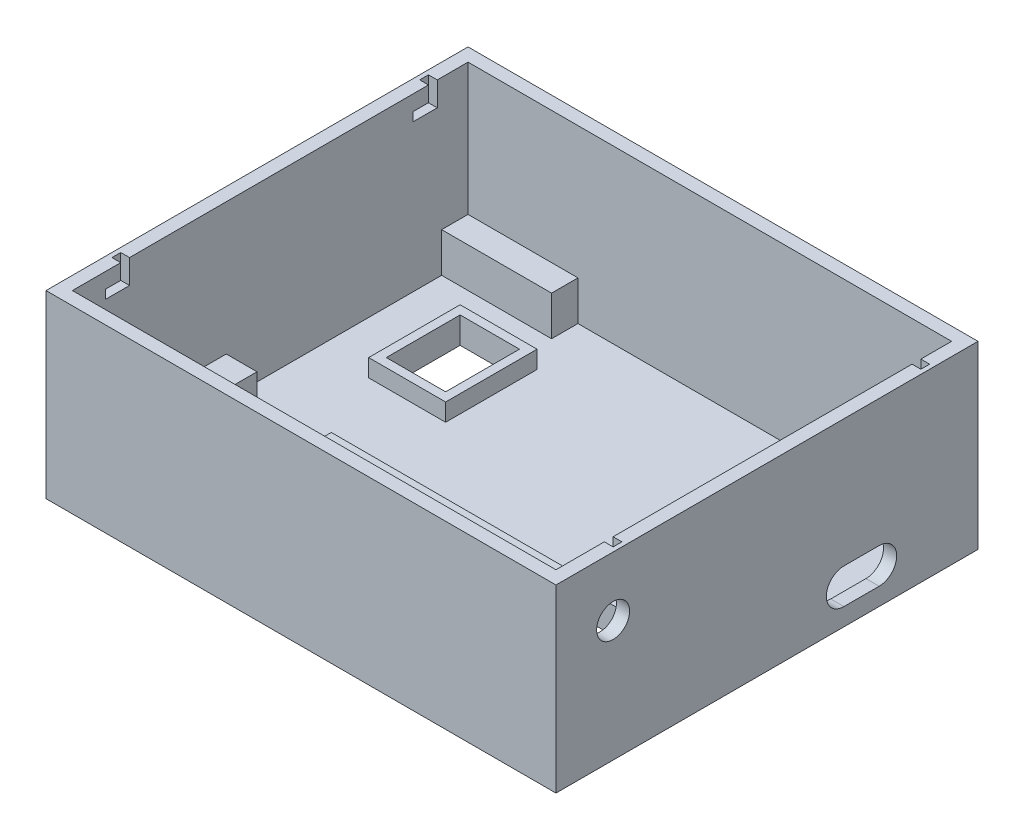
SolidWorks part; units mm, degrees
ref_plane "Front Plane" through (0, 0, 0) normal (0, 0, 1) x (1, 0, 0)
ref_plane "Top Plane" through (0, 0, 0) normal (0, 1, 0) x (1, 0, 0)
ref_plane "Right Plane" through (0, 0, 0) normal (1, 0, 0) x (0, 0, -1)
sketch "Sketch1" plane through (0, 0, 0) normal (0, 1, 0) x (1, 0, 0)
  line L1 (-58, 48) -> (58, 48)
  line L2 (-58, 48) -> (-58, -48)
  line L3 (-58, -48) -> (58, -48)
  line L4 (58, 48) -> (58, -48)
  line L5 (-58, 48) -> (58, -48) construction
  line L6 (-58, -48) -> (58, 48) construction
  point P0 (0, 0)
  dimension "D1" = 116
  dimension "D2" = 96
extrude "Boss-Extrude1" add sketch "Sketch1" along normal blind 6
sketch "Sketch2" plane through (0, 6, 0) normal (0, 1, 0) x (1, 0, 0)
  line L0 (58, 48) -> (-58, 48) construction
  line L1 (-58, -48) -> (58, -48)
  line L2 (-58, -48) -> (-58, 48)
  line L3 (-58, 48) -> (58, 48)
  line L4 (58, -48) -> (58, 48)
  line L5 (-58, -48) -> (58, 48) construction
  line L6 (-58, 48) -> (58, -48) construction
  line L7 (58, -48) -> (58, 48) construction
  line L9 (-55, 45) -> (55, 45)
  line L10 (-55, 45) -> (-55, -45)
  line L11 (-55, -45) -> (55, -45)
  line L12 (55, 45) -> (55, -45)
  line L13 (-55, 45) -> (55, -45) construction
  line L14 (-55, -45) -> (55, 45) construction
  point P0 (0, 0)
  point P10 (0, 0)
  dimension "D1" = 3
  dimension "D2" = 3
extrude "Boss-Extrude2" add sketch "Sketch2" along normal blind 35
sketch "Sketch3" plane through (0, 6, 0) normal (0, 1, 0) x (1, 0, 0)
  line L0 (-55, -45) -> (55, -45) construction
  line L1 (-25.6, -10.5) -> (46, -10.5)
  line L2 (-25.6, -10.5) -> (-25.6, -35)
  line L3 (-25.6, -35) -> (46, -35)
  line L4 (46, -10.5) -> (46, -35)
  line L5 (55, -45) -> (55, 45) construction
  line L7 (-41.1, 29.3) -> (-27.6, 29.3)
  line L8 (-41.1, 29.3) -> (-41.1, 12.5)
  line L9 (-41.1, 12.5) -> (-27.6, 12.5)
  line L10 (-27.6, 29.3) -> (-27.6, 12.5)
  dimension "D1" = 24.5
  dimension "D2" = 71.6
  dimension "D3" = 10
  dimension "D4" = 9
  dimension "D5" = 23
  dimension "D6" = 2
  dimension "D7" = 16.8
  dimension "D8" = 13.5
extrude "Cut-Extrude1" cut sketch "Sketch3" against normal blind 35
sketch "Sketch4" plane through (0, 6, 0) normal (0, 1, 0) x (1, 0, 0)
  line L0 (-25.6, -10.5) -> (-25.6, -35) construction
  line L1 (-30.6, -13.75) -> (-25.6, -13.75)
  line L2 (-30.6, -13.75) -> (-30.6, -31.75)
  line L3 (-30.6, -31.75) -> (-25.6, -31.75)
  line L4 (-25.6, -13.75) -> (-25.6, -31.75)
  point P6 (-25.6, -22.75)
  point P7 (-25.6, -22.75)
  dimension "D1" = 18
  dimension "D2" = 5
extrude "Cut-Extrude2" cut sketch "Sketch4" against normal blind 4
sketch "Sketch5" plane through (0, 0, 0) normal (0, 1, 0) x (1, 0, 0)
  line L0 (0, 9.4044) -> (0, -19.4219) construction
  line L1 (0, -10.5) -> (71.4405, -10.5) construction
  line L2 (46, -10.5) -> (-25.6, -10.5) construction
sketch "Sketch6" plane through (58, 0, 0) normal (1, 0, 0) x (0, 0, -1)
  line L0 (17.5, 8) -> (25.5, 8) construction
  line L1 (17.5, 12) -> (25.5, 12)
  line L2 (17.5, 4) -> (25.5, 4)
  line L3 (9.4044, 0) -> (-19.4219, 0) construction
  arc A0 (17.5, 12) -> (17.5, 4) centre (17.5, 8) ccw
  arc A1 (25.5, 4) -> (25.5, 12) centre (25.5, 8) ccw
  circle A2 centre (-35, 27.5002) radius 3.75
  point P2 (21.5, 8)
  dimension "D4" = 4
  dimension "D5" = 7.5
  dimension "D1" = 8
  dimension "D2" = 28
  dimension "D3" = 8
  dimension "D6" = 27.5002
  dimension "D7" = 35
extrude "Cut-Extrude3" cut sketch "Sketch6" against normal blind 3
sketch "Sketch7" plane through (0, 6, 0) normal (0, 1, 0) x (1, 0, 0)
  line L0 (0, -10.5) -> (71.4405, -10.5) construction
  line L1 (-32.6, -8.5) -> (48, -8.5)
  line L2 (-32.6, -8.5) -> (-32.6, -37)
  line L3 (-32.6, -37) -> (48, -37)
  line L4 (48, -8.5) -> (48, -37)
  line L5 (-25.6, -35) -> (46, -35) construction
  line L6 (46, -35) -> (46, -10.5) construction
  line L7 (-30.6, -13.75) -> (-30.6, -31.75) construction
  line L8 (-27.6, 29.3) -> (-41.1, 29.3) construction
  line L9 (-43.1, 31.3) -> (-25.6, 31.3)
  line L10 (-43.1, 31.3) -> (-43.1, 10.5)
  line L11 (-43.1, 10.5) -> (-25.6, 10.5)
  line L12 (-25.6, 31.3) -> (-25.6, 10.5)
  line L13 (-27.6, 12.5) -> (-27.6, 29.3) construction
  line L14 (-41.1, 12.5) -> (-27.6, 12.5) construction
  line L15 (-41.1, 29.3) -> (-41.1, 12.5) construction
  line L17 (-55, 45) -> (55, 45)
  line L18 (-55, 45) -> (-55, -45)
  line L19 (-55, -45) -> (55, -45)
  line L20 (55, 45) -> (55, -45)
  dimension "D1" = 2
  dimension "D2" = 2
  dimension "D3" = 2
  dimension "D4" = 2
  dimension "D5" = 2
  dimension "D6" = 2
  dimension "D7" = 2
  dimension "D8" = 2
extrude "Cut-Extrude4" cut sketch "Sketch7" against normal blind 4
sketch "Sketch8" plane through (0, 2, 0) normal (0, 1, 0) x (1, 0, 0)
  line L0 (-55, 45) -> (-55, -45) construction
  line L1 (-55, -10) -> (-48, -10)
  line L2 (-55, -10) -> (-55, -45)
  line L3 (-55, -45) -> (-48, -45)
  line L4 (-48, -10) -> (-48, -45)
  line L5 (-55, -45) -> (55, -45) construction
  line L7 (55, 45) -> (40, 45)
  line L8 (55, 45) -> (55, 39)
  line L9 (55, 39) -> (40, 39)
  line L10 (40, 45) -> (40, 39)
  line L11 (-55, 45) -> (-30, 45)
  line L12 (-55, 45) -> (-55, 39)
  line L13 (-55, 39) -> (-30, 39)
  line L14 (-30, 45) -> (-30, 39)
  dimension "D1" = 7
  dimension "D2" = 35
  dimension "D3" = 15
  dimension "D4" = 6
  dimension "D5" = 6
  dimension "D6" = 25
extrude "Boss-Extrude3" add sketch "Sketch8" along normal blind 9
sketch "Sketch10" plane through (58, 0, 0) normal (1, 0, 0) x (0, 0, -1)
  line L0 (-32, 41) -> (-32, 35.5)
  line L1 (-48, 41) -> (48, 41) construction
  line L2 (-32, 35.5) -> (-37.5, 35.5)
  line L3 (-37.5, 35.5) -> (-37.5, 37.5)
  line L4 (-37.5, 37.5) -> (-34, 37.5)
  line L5 (-34, 37.5) -> (-34, 41)
  line L6 (-34, 41) -> (-32, 41)
  line L7 (-48, 0) -> (48, 0) construction
  line L8 (0, 0) -> (0, 53.1609) construction
  line L9 (36, 41) -> (38, 41)
  line L10 (38, 41) -> (38, 35.5)
  line L11 (38, 35.5) -> (32.5, 35.5)
  line L12 (32.5, 35.5) -> (32.5, 37.5)
  line L13 (32.5, 37.5) -> (36, 37.5)
  line L14 (36, 37.5) -> (36, 41)
  line L15 (70, 0) -> (70, 53.1609) construction
  dimension "D1" = 2
  dimension "D2" = 2
  dimension "D3" = 3.5
  dimension "D4" = 3.5
  dimension "D5" = 35.5
  dimension "D6" = 32
  dimension "D7" = 2
extrude "Cut-Extrude6" cut sketch "Sketch10" against normal blind 114 from offset 1
